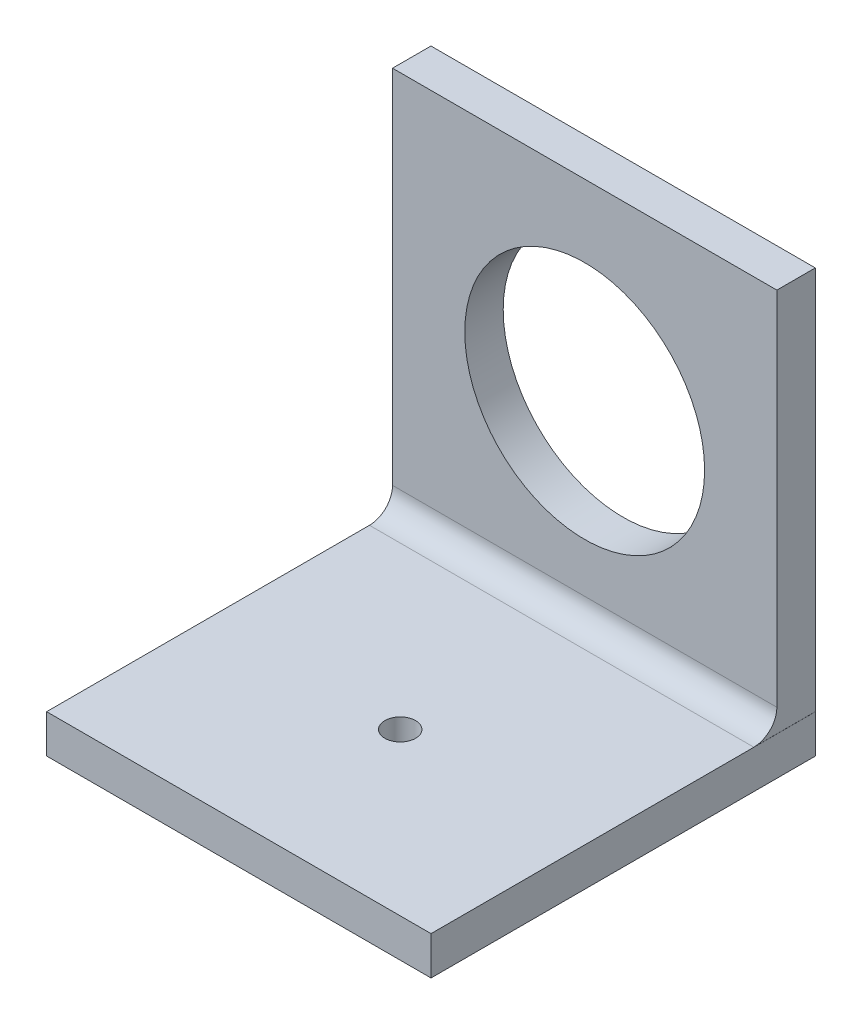
SolidWorks part; units mm, degrees
ref_plane "Plano frontal" through (0, 0, 0) normal (0, 0, 1) x (1, 0, 0)
ref_plane "Plano superior" through (0, 0, 0) normal (0, 1, 0) x (1, 0, 0)
ref_plane "Plano direito" through (0, 0, 0) normal (1, 0, 0) x (0, 0, -1)
sketch "Esboço1" plane through (0, 0, 0) normal (0, 0, 1) x (1, 0, 0)
  line L1 (0, 0) -> (50, 0)
  line L2 (0, 0) -> (0, 50)
  line L3 (0, 50) -> (50, 50)
  line L4 (50, 0) -> (50, 50)
  dimension "D1" = 50
  dimension "D2" = 50
extrude "Ressalto-extrusão1" add sketch "Esboço1" along normal blind 5
sketch "Esboço2" plane through (0, 0, 0) normal (0, 0, 1) x (1, 0, 0)
  line L1 (50, 0) -> (50, 50) construction
  circle A0 centre (25, 25) radius 15.6
  dimension "D1" = 31.2
extrude "Corte-extrusão1" cut sketch "Esboço2" along normal blind 8 and the other way blind 14
sketch "Esboço3" plane through (0, 0, 0) normal (0, 0, 1) x (1, 0, 0)
  line L1 (0, 0) -> (50.011, 0)
  line L2 (0, 0) -> (0, -5)
  line L3 (0, -5) -> (50.011, -5)
  line L4 (50.011, 0) -> (50.011, -5)
  dimension "D1" = 5
extrude "Ressalto-extrusão2" add sketch "Esboço3" along normal blind 50
fillet "Filete1" radius 3 1 edges
sketch "Esboço5" plane through (0, 0, 0) normal (0, 1, 0) x (1, 0, 0)
  line L0 (25.0055, -50) -> (25, -8) construction
  line L1 (50.011, -50) -> (0, -50) construction
  line L2 (50, -8) -> (0, -8) construction
  line L3 (25, -8) -> (0, -8) construction
  line L4 (0, -8) -> (50.011, -50) construction
  circle A0 centre (25.0028, -29) radius 2
  dimension "D1" = 4
extrude "Corte-extrusão4" cut sketch "Esboço5" against normal blind 14
